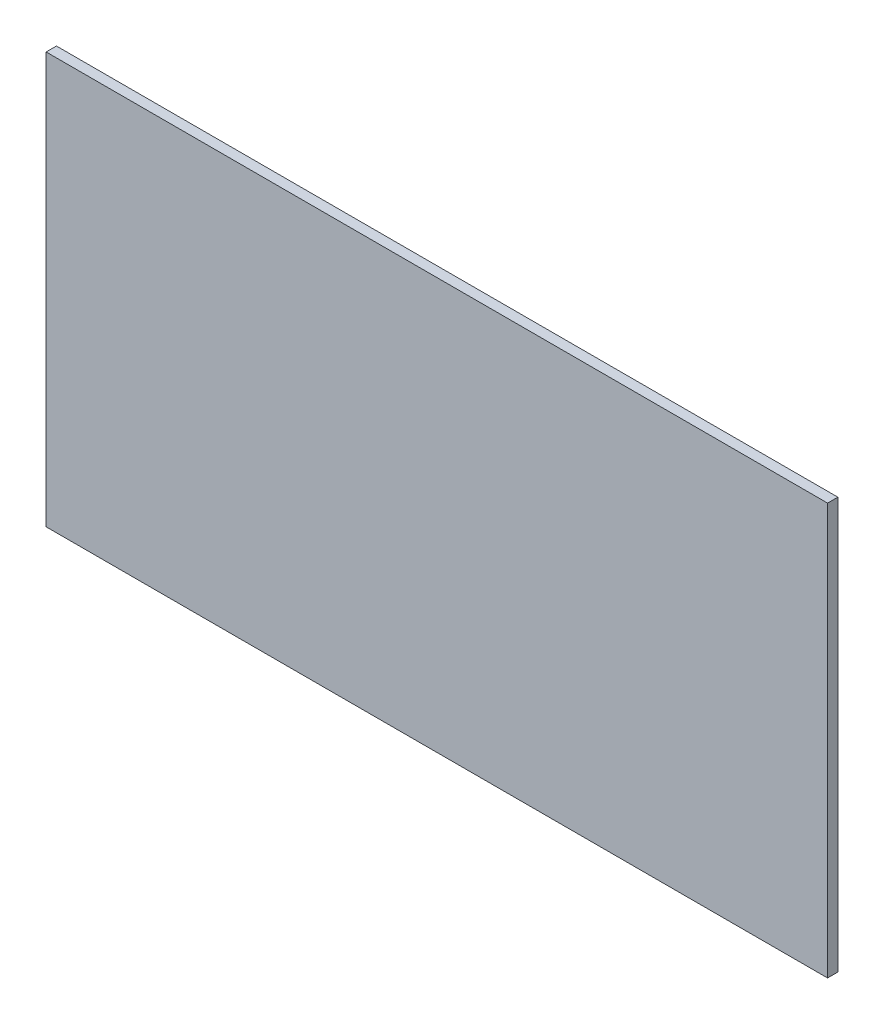
SolidWorks part; units mm, degrees
ref_plane "Front Plane" through (0, 0, 0) normal (0, 0, 1) x (1, 0, 0)
ref_plane "Top Plane" through (0, 0, 0) normal (0, 1, 0) x (1, 0, 0)
ref_plane "Right Plane" through (0, 0, 0) normal (1, 0, 0) x (0, 0, -1)
sketch "Sketch1" plane through (0, 0, 0) normal (1, 0, 0) x (0, 0, -1)
  line L1 (0, 0) -> (3.175, 0)
  line L2 (0, 0) -> (0, 127)
  line L3 (0, 127) -> (3.175, 127)
  line L4 (3.175, 0) -> (3.175, 127)
  dimension "D1" = 127
  dimension "D2" = 3.175
extrude "Boss-Extrude1" add sketch "Sketch1" along normal blind 241.3
